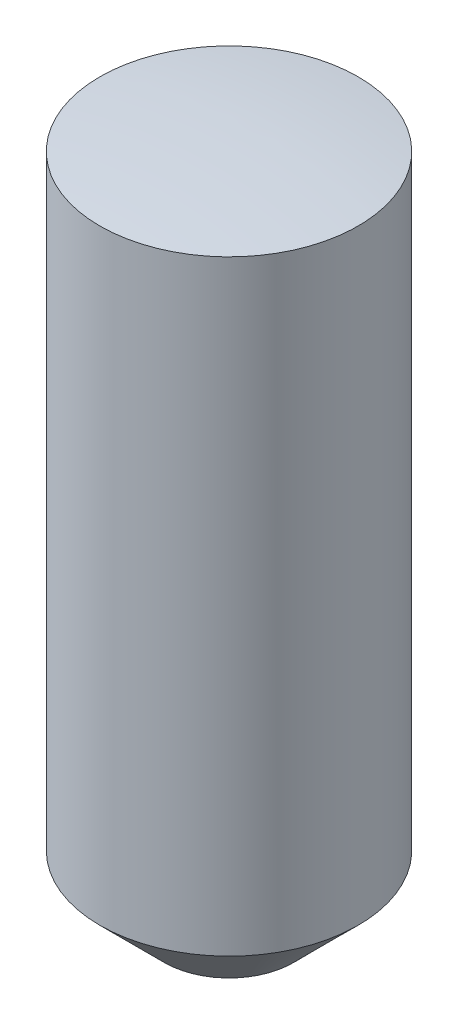
SolidWorks part; units mm, degrees
ref_plane "Front Plane" through (0, 0, 0) normal (0, 0, 1) x (1, 0, 0)
ref_plane "Top Plane" through (0, 0, 0) normal (0, 1, 0) x (1, 0, 0)
ref_plane "Right Plane" through (0, 0, 0) normal (1, 0, 0) x (0, 0, -1)
sketch "Sketch1" plane through (0, 0, 0) normal (0, 1, 0) x (1, 0, 0)
  circle A0 centre (0, 0) radius 1
  dimension "D1" = 2
extrude "Boss-Extrude 5.25mm" add sketch "Sketch1" against normal blind 5.25
chamfer "0.5 x 45 deg" distance 0.5 angle 45 1 edges at (0, -5.25, 1)
sketch "Sketch2" plane through (0, 0, 0) normal (0, 0, 1) x (1, 0, 0)
  line L0 (0, 0) -> (0, 2) construction
  line L1 (0, 2) -> (-2, 2)
  line L2 (-2, 2) -> (-2, -0.254)
  line L3 (0, 0) -> (0, 2)
  arc A0 (0, 0) -> (-2, -0.254) centre (0, -8) ccw
  dimension "D3" = 8
  dimension "D1" = 2
  dimension "D2" = 2
revolve "SR8" cut sketch "Sketch2" angle 360 about L0
